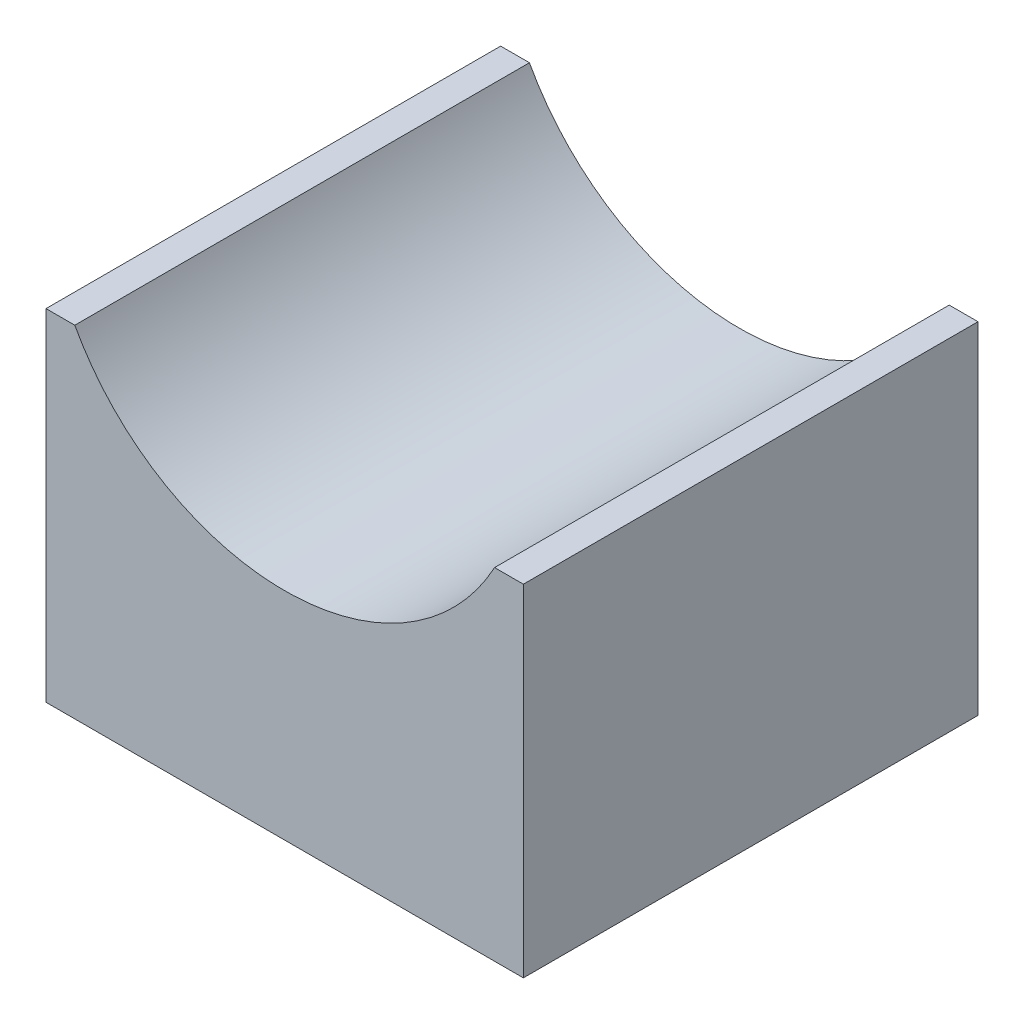
SolidWorks part; units mm, degrees
material "ABS"
ref_plane "前视基准面" through (0, 0, 0) normal (0, 0, 1) x (1, 0, 0)
ref_plane "上视基准面" through (0, 0, 0) normal (0, 1, 0) x (1, 0, 0)
ref_plane "右视基准面" through (0, 0, 0) normal (1, 0, 0) x (0, 0, -1)
sketch "草图1" plane through (0, 0, 0) normal (0, 0, 1) x (1, 0, 0)
  line L0 (0, 0) -> (0, 20) construction
  line L1 (-10.5, 15) -> (-10.5, 0)
  line L2 (-10.5, 0) -> (10.5, 0)
  line L3 (10.5, 0) -> (10.5, 15)
  line L4 (9.2331, 15) -> (10.5, 15)
  line L5 (-10.5, 15) -> (-9.2331, 15)
  arc A0 (-9.2331, 15) -> (9.2331, 15) centre (0, 20) ccw
extrude "凸台-拉伸1" add sketch "草图1" along normal mid plane 20
